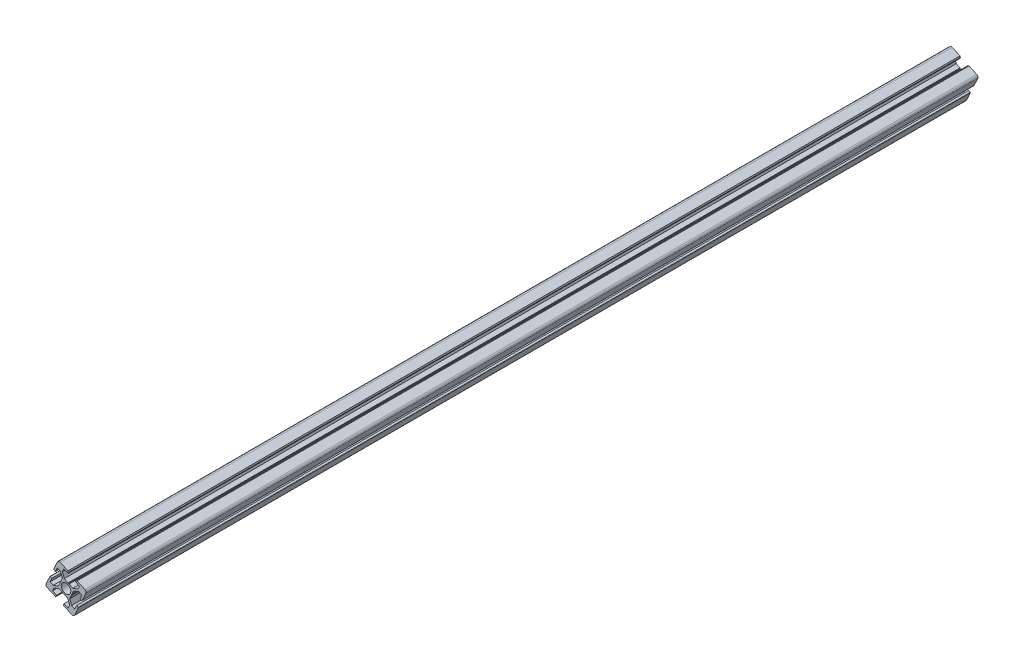
SolidWorks part; units mm, degrees
material "1060 Alloy"
ref_plane "Front" through (0, 0, 0) normal (0, 0, 1) x (1, 0, 0)
ref_plane "Top" through (0, 0, 0) normal (0, 1, 0) x (1, 0, 0)
ref_plane "Right" through (0, 0, 0) normal (1, 0, 0) x (0, 0, -1)
sketch "Sketch1" plane through (0, 0, 0) normal (0, 0, 1) x (1, 0, 0)
  line L0 (-8.2163, 18.0691) -> (-11.8426, 10.1609)
  line L1 (-11.6949, 9.7631) -> (-10.1496, 9.0546)
  line L2 (-10.1496, 9.0546) -> (-8.3782, 12.9178)
  line L3 (-8.3782, 12.9178) -> (-5.346, 11.5274)
  line L4 (-5.346, 11.5274) -> (-3.5425, 6.6693)
  line L5 (-3.5425, 6.6693) -> (-5.2374, 2.9732)
  line L6 (-5.2374, 2.9732) -> (-5.1813, 2.3758)
  line L7 (-5.1813, 2.3758) -> (-5.6705, 2.0286)
  line L8 (-5.6705, 2.0286) -> (-7.3654, -1.6675)
  line L9 (-7.3654, -1.6675) -> (-12.2234, -3.471)
  line L10 (-12.2234, -3.471) -> (-15.2556, -2.0806)
  line L11 (-15.2556, -2.0806) -> (-13.4841, 1.7826)
  line L12 (-13.4841, 1.7826) -> (-15.0294, 2.4912)
  line L13 (-15.4272, 2.3436) -> (-19.0535, -5.5647)
  line L14 (-18.0691, -8.2163) -> (-10.1609, -11.8426)
  line L15 (-9.7631, -11.6949) -> (-9.0546, -10.1496)
  line L16 (-9.0546, -10.1496) -> (-12.9178, -8.3782)
  line L17 (-12.9178, -8.3782) -> (-11.5274, -5.346)
  line L18 (-11.5274, -5.346) -> (-6.6693, -3.5425)
  line L19 (-6.6693, -3.5425) -> (-2.9732, -5.2374)
  line L20 (-2.9732, -5.2374) -> (-2.3758, -5.1813)
  line L21 (1.9074, 15.6272) -> (-5.5647, 19.0535)
  line L22 (2.3758, 5.1813) -> (2.9732, 5.2374)
  line L23 (2.9732, 5.2374) -> (6.6693, 3.5425)
  line L24 (12.9178, 8.3782) -> (8.9517, 10.1968)
  line L26 (10.597, 11.6426) -> (18.0691, 8.2163)
  line L27 (11.5274, 5.346) -> (12.9178, 8.3782)
  line L28 (6.6693, 3.5425) -> (11.5274, 5.346)
  line L29 (-2.0286, -5.6705) -> (-2.3758, -5.1813)
  line L30 (1.6675, -7.3654) -> (-2.0286, -5.6705)
  line L31 (3.471, -12.2234) -> (1.6675, -7.3654)
  line L32 (2.0806, -15.2556) -> (3.471, -12.2234)
  line L33 (-1.7826, -13.4841) -> (2.0806, -15.2556)
  line L34 (2.3758, 5.1813) -> (2.0286, 5.6705)
  line L35 (2.0286, 5.6705) -> (-1.6675, 7.3654)
  line L36 (-1.6675, 7.3654) -> (-3.471, 12.2234)
  line L37 (-3.471, 12.2234) -> (-2.0806, 15.2556)
  line L38 (-2.0806, 15.2556) -> (1.8855, 13.437)
  line L40 (2.3758, 5.1813) -> (-2.3758, -5.1813) construction
  line L41 (-2.4912, -15.0294) -> (-1.7826, -13.4841)
  line L42 (5.5647, -19.0535) -> (-2.3436, -15.4272)
  line L43 (11.8426, -10.1609) -> (8.2163, -18.0691)
  line L44 (10.1496, -9.0546) -> (11.6949, -9.7631)
  line L45 (8.3782, -12.9178) -> (10.1496, -9.0546)
  line L46 (5.346, -11.5274) -> (8.3782, -12.9178)
  line L47 (3.5425, -6.6693) -> (5.346, -11.5274)
  line L48 (5.2374, -2.9732) -> (3.5425, -6.6693)
  line L49 (5.1813, -2.3758) -> (5.2374, -2.9732)
  line L50 (5.6705, -2.0286) -> (5.1813, -2.3758)
  line L51 (7.3654, 1.6675) -> (5.6705, -2.0286)
  line L52 (12.2234, 3.471) -> (7.3654, 1.6675)
  line L53 (15.2556, 2.0806) -> (12.2234, 3.471)
  line L54 (13.4841, -1.7826) -> (15.2556, 2.0806)
  line L55 (15.0294, -2.4912) -> (13.4841, -1.7826)
  line L56 (19.0535, 5.5647) -> (15.4272, -2.3436)
  line L57 (1.8855, 13.437) -> (2.3469, 14.4432)
  line L58 (2.3469, 14.4432) -> (1.9074, 15.6272)
  line L59 (8.9517, 10.1968) -> (9.4131, 11.2031)
  line L60 (9.4131, 11.2031) -> (10.597, 11.6426)
  arc A0 (-5.5647, 19.0535) -> (-8.2163, 18.0691) centre (-6.3983, 17.2355) ccw
  arc A1 (-11.8426, 10.1609) -> (-11.6949, 9.7631) centre (-11.5699, 10.0358) ccw
  arc A2 (-15.0294, 2.4912) -> (-15.4272, 2.3436) centre (-15.1545, 2.2185) ccw
  arc A3 (-19.0535, -5.5647) -> (-18.0691, -8.2163) centre (-17.2355, -6.3983) ccw
  arc A4 (-10.1609, -11.8426) -> (-9.7631, -11.6949) centre (-10.0358, -11.5699) ccw
  arc A6 (-2.3436, -15.4272) -> (-2.4912, -15.0294) centre (-2.2185, -15.1545) cw
  arc A7 (8.2163, -18.0691) -> (5.5647, -19.0535) centre (6.3983, -17.2355) cw
  arc A8 (11.6949, -9.7631) -> (11.8426, -10.1609) centre (11.5699, -10.0358) cw
  arc A10 (15.4272, -2.3436) -> (15.0294, -2.4912) centre (15.1545, -2.2185) cw
  arc A11 (18.0691, 8.2163) -> (19.0535, 5.5647) centre (17.2355, 6.3983) cw
  dimension "D1" = 45
  dimension "D2" = 30
extrude "Boss-Extrude1" add sketch "Sketch1" along normal blind 2000
scale "Scale1" scale about centroid uniform scaling yes scale factor 3
sketch "Sketch2" plane through (0, 0, -2000) normal (0, 0, -1) x (-1, 0, 0)
  circle A0 centre (0, 0) radius 115.0478
extrude "Cut-Extrude1" cut sketch "Sketch2" against normal blind 1600
sketch "Sketch3" plane through (0, 0, 4000) normal (0, 0, 1) x (1, 0, 0)
  circle A0 centre (0, 0) radius 13.75
  dimension "D1" = 27.5
extrude "Cut-Extrude2" cut sketch "Sketch3" against normal through all
scale "Scale2" bodies to scale 104 scale about centroid uniform scaling yes scale factor 0.466667
sketch "Sketch6" plane through (0, 0, 773.3333) normal (0, 0, -1) x (-1, 0, 0)
  line L58 (7.7891, 26.678) -> (-2.6718, 21.8811)
  line L59 (-2.6718, 21.8811) -> (-3.2872, 20.2236)
  line L60 (-3.2872, 20.2236) -> (-2.6412, 18.8149)
  line L61 (-2.6412, 18.8149) -> (2.9114, 21.361)
  line L62 (2.9114, 21.361) -> (4.858, 17.1159)
  line L63 (4.858, 17.1159) -> (2.3331, 10.3146)
  line L64 (2.3331, 10.3146) -> (-2.8414, 7.9419)
  line L65 (-2.8414, 7.9419) -> (-3.3276, 7.2569)
  line L66 (-3.3276, 7.2569) -> (-4.1639, 7.3354)
  line L67 (-4.1639, 7.3354) -> (-9.3385, 4.9626)
  line L68 (-9.3385, 4.9626) -> (-16.1397, 7.4875)
  line L69 (-16.1397, 7.4875) -> (-18.0863, 11.7325)
  line L70 (-18.0863, 11.7325) -> (-12.5338, 14.2786)
  line L71 (-12.5338, 14.2786) -> (-13.1797, 15.6874)
  line L72 (-13.1797, 15.6874) -> (-14.8373, 16.3027)
  line L73 (-14.8373, 16.3027) -> (-25.2982, 11.5059)
  line L74 (-26.6763, 7.7936) -> (-21.5995, -3.2779)
  line L75 (-21.0426, -3.4846) -> (-18.8792, -2.4926)
  line L76 (-18.8792, -2.4926) -> (-21.3593, 2.9159)
  line L77 (-21.3593, 2.9159) -> (-17.1142, 4.8625)
  line L78 (-17.1142, 4.8625) -> (-10.3129, 2.3377)
  line L79 (-10.3129, 2.3377) -> (-7.9402, -2.8369)
  line L80 (-7.9402, -2.8369) -> (-7.2552, -3.3231)
  line L81 (-7.2552, -3.3231) -> (-7.3337, -4.1594)
  line L82 (-7.3337, -4.1594) -> (-4.961, -9.334)
  line L83 (-4.961, -9.334) -> (-7.4858, -16.1352)
  line L84 (-7.4858, -16.1352) -> (-11.7309, -18.0818)
  line L85 (-11.7309, -18.0818) -> (-14.2109, -12.6733)
  line L86 (-14.2109, -12.6733) -> (-16.3743, -13.6653)
  line L87 (-16.581, -14.2221) -> (-11.5042, -25.2936)
  line L88 (-7.7919, -26.6717) -> (3.2796, -21.5949)
  line L89 (3.4863, -21.0381) -> (2.4943, -18.8747)
  line L90 (2.4943, -18.8747) -> (-2.9142, -21.3547)
  line L91 (-2.9142, -21.3547) -> (-4.8608, -17.1097)
  line L92 (-4.8608, -17.1097) -> (-2.336, -10.3084)
  line L93 (-2.336, -10.3084) -> (2.8386, -7.9356)
  line L94 (2.8386, -7.9356) -> (3.3248, -7.2506)
  line L95 (3.3248, -7.2506) -> (4.1611, -7.3292)
  line L96 (4.1611, -7.3292) -> (9.3356, -4.9564)
  line L97 (9.3356, -4.9564) -> (16.1369, -7.4812)
  line L98 (16.1369, -7.4812) -> (18.0835, -11.7263)
  line L99 (18.0835, -11.7263) -> (12.675, -14.2064)
  line L100 (12.675, -14.2064) -> (13.667, -16.3698)
  line L101 (14.2238, -16.5765) -> (25.2953, -11.4997)
  line L102 (26.6734, -7.7874) -> (21.5966, 3.2841)
  line L103 (21.0398, 3.4908) -> (18.8764, 2.4988)
  line L104 (18.8764, 2.4988) -> (21.3564, -2.9097)
  line L105 (21.3564, -2.9097) -> (17.1113, -4.8563)
  line L106 (17.1113, -4.8563) -> (10.3101, -2.3315)
  line L107 (10.3101, -2.3315) -> (7.9373, 2.8431)
  line L108 (7.9373, 2.8431) -> (7.2523, 3.3293)
  line L109 (7.2523, 3.3293) -> (7.3309, 4.1656)
  line L110 (7.3309, 4.1656) -> (4.9581, 9.3402)
  line L111 (4.9581, 9.3402) -> (7.4829, 16.1414)
  line L112 (7.4829, 16.1414) -> (11.728, 18.088)
  line L113 (11.728, 18.088) -> (14.208, 12.6795)
  line L114 (14.208, 12.6795) -> (16.3714, 13.6715)
  line L115 (16.5782, 14.2284) -> (11.5014, 25.2999)
  line L116 (7.7891, 26.678) -> (-2.6718, 21.8811)
  line L117 (-2.6718, 21.8811) -> (-3.2872, 20.2236)
  line L118 (-3.2872, 20.2236) -> (-2.6412, 18.8149)
  line L119 (-2.6412, 18.8149) -> (2.9114, 21.361)
  line L120 (2.9114, 21.361) -> (4.858, 17.1159)
  line L121 (4.858, 17.1159) -> (2.3331, 10.3146)
  line L122 (2.3331, 10.3146) -> (-2.8414, 7.9419)
  line L123 (-2.8414, 7.9419) -> (-3.3276, 7.2569)
  line L124 (-3.3276, 7.2569) -> (-4.1639, 7.3354)
  line L125 (-4.1639, 7.3354) -> (-9.3385, 4.9626)
  line L126 (-9.3385, 4.9626) -> (-16.1397, 7.4875)
  line L127 (-16.1397, 7.4875) -> (-18.0863, 11.7325)
  line L128 (-18.0863, 11.7325) -> (-12.5338, 14.2786)
  line L129 (-12.5338, 14.2786) -> (-13.1797, 15.6874)
  line L130 (-13.1797, 15.6874) -> (-14.8373, 16.3027)
  line L131 (-14.8373, 16.3027) -> (-25.2982, 11.5059)
  line L132 (-26.6763, 7.7936) -> (-21.5995, -3.2779)
  line L133 (-21.0426, -3.4846) -> (-18.8792, -2.4926)
  line L134 (-18.8792, -2.4926) -> (-21.3593, 2.9159)
  line L135 (-21.3593, 2.9159) -> (-17.1142, 4.8625)
  line L136 (-17.1142, 4.8625) -> (-10.3129, 2.3377)
  line L137 (-10.3129, 2.3377) -> (-7.9402, -2.8369)
  line L138 (-7.9402, -2.8369) -> (-7.2552, -3.3231)
  line L139 (-7.2552, -3.3231) -> (-7.3337, -4.1594)
  line L140 (-7.3337, -4.1594) -> (-4.961, -9.334)
  line L141 (-4.961, -9.334) -> (-7.4858, -16.1352)
  line L142 (-7.4858, -16.1352) -> (-11.7309, -18.0818)
  line L143 (-11.7309, -18.0818) -> (-14.2109, -12.6733)
  line L144 (-14.2109, -12.6733) -> (-16.3743, -13.6653)
  line L145 (-16.581, -14.2221) -> (-11.5042, -25.2936)
  line L146 (-7.7919, -26.6717) -> (3.2796, -21.5949)
  line L147 (3.4863, -21.0381) -> (2.4943, -18.8747)
  line L148 (2.4943, -18.8747) -> (-2.9142, -21.3547)
  line L149 (-2.9142, -21.3547) -> (-4.8608, -17.1097)
  line L150 (-4.8608, -17.1097) -> (-2.336, -10.3084)
  line L151 (-2.336, -10.3084) -> (2.8386, -7.9356)
  line L152 (2.8386, -7.9356) -> (3.3248, -7.2506)
  line L153 (3.3248, -7.2506) -> (4.1611, -7.3292)
  line L154 (4.1611, -7.3292) -> (9.3356, -4.9564)
  line L155 (9.3356, -4.9564) -> (16.1369, -7.4812)
  line L156 (16.1369, -7.4812) -> (18.0835, -11.7263)
  line L157 (18.0835, -11.7263) -> (12.675, -14.2064)
  line L158 (12.675, -14.2064) -> (13.667, -16.3698)
  line L159 (14.2238, -16.5765) -> (25.2953, -11.4997)
  line L160 (26.6734, -7.7874) -> (21.5966, 3.2841)
  line L161 (21.0398, 3.4908) -> (18.8764, 2.4988)
  line L162 (18.8764, 2.4988) -> (21.3564, -2.9097)
  line L163 (21.3564, -2.9097) -> (17.1113, -4.8563)
  line L164 (17.1113, -4.8563) -> (10.3101, -2.3315)
  line L165 (10.3101, -2.3315) -> (7.9373, 2.8431)
  line L166 (7.9373, 2.8431) -> (7.2523, 3.3293)
  line L167 (7.2523, 3.3293) -> (7.3309, 4.1656)
  line L168 (7.3309, 4.1656) -> (4.9581, 9.3402)
  line L169 (4.9581, 9.3402) -> (7.4829, 16.1414)
  line L170 (7.4829, 16.1414) -> (11.728, 18.088)
  line L171 (11.728, 18.088) -> (14.208, 12.6795)
  line L172 (14.208, 12.6795) -> (16.3714, 13.6715)
  line L173 (16.5782, 14.2284) -> (11.5014, 25.2999)
  arc A10 (11.5014, 25.2999) -> (7.7891, 26.678) centre (8.9562, 24.1328) ccw
  arc A11 (-25.2982, 11.5059) -> (-26.6763, 7.7936) centre (-24.1311, 8.9607) ccw
  arc A12 (-21.5995, -3.2779) -> (-21.0426, -3.4846) centre (-21.2177, -3.1028) ccw
  arc A13 (-16.3743, -13.6653) -> (-16.581, -14.2221) centre (-16.1992, -14.0471) ccw
  arc A14 (-11.5042, -25.2936) -> (-7.7919, -26.6717) centre (-8.959, -24.1266) ccw
  arc A15 (3.2796, -21.5949) -> (3.4863, -21.0381) centre (3.1045, -21.2132) ccw
  arc A16 (13.667, -16.3698) -> (14.2238, -16.5765) centre (14.0488, -16.1947) ccw
  arc A17 (25.2953, -11.4997) -> (26.6734, -7.7874) centre (24.1282, -8.9545) ccw
  arc A18 (21.5966, 3.2841) -> (21.0398, 3.4908) centre (21.2148, 3.109) ccw
  arc A19 (16.3714, 13.6715) -> (16.5782, 14.2284) centre (16.1964, 14.0533) ccw
  arc A20 (11.5014, 25.2999) -> (7.7891, 26.678) centre (8.9562, 24.1328) ccw
  arc A21 (-25.2982, 11.5059) -> (-26.6763, 7.7936) centre (-24.1311, 8.9607) ccw
  arc A22 (-21.5995, -3.2779) -> (-21.0426, -3.4846) centre (-21.2177, -3.1028) ccw
  arc A23 (-16.3743, -13.6653) -> (-16.581, -14.2221) centre (-16.1992, -14.0471) ccw
  arc A24 (-11.5042, -25.2936) -> (-7.7919, -26.6717) centre (-8.959, -24.1266) ccw
  arc A25 (3.2796, -21.5949) -> (3.4863, -21.0381) centre (3.1045, -21.2132) ccw
  arc A26 (13.667, -16.3698) -> (14.2238, -16.5765) centre (14.0488, -16.1947) ccw
  arc A27 (25.2953, -11.4997) -> (26.6734, -7.7874) centre (24.1282, -8.9545) ccw
  arc A28 (21.5966, 3.2841) -> (21.0398, 3.4908) centre (21.2148, 3.109) ccw
  arc A29 (16.3714, 13.6715) -> (16.5782, 14.2284) centre (16.1964, 14.0533) ccw
  dimension "D1" = 0
extrude "Cut-Extrude3" cut sketch "Sketch6" against normal blind 53.3
sketch "Sketch7" plane through (0, 0, 826.6333) normal (0, 0, -1) x (-1, 0, 0)
  line L58 (7.7891, 26.678) -> (-2.6718, 21.8811)
  line L59 (-2.6718, 21.8811) -> (-3.2872, 20.2236)
  line L60 (-3.2872, 20.2236) -> (-2.6412, 18.8149)
  line L61 (-2.6412, 18.8149) -> (2.9114, 21.361)
  line L62 (2.9114, 21.361) -> (4.858, 17.1159)
  line L63 (4.858, 17.1159) -> (2.3331, 10.3146)
  line L64 (2.3331, 10.3146) -> (-2.8414, 7.9419)
  line L65 (-2.8414, 7.9419) -> (-3.3276, 7.2569)
  line L66 (-3.3276, 7.2569) -> (-4.1639, 7.3354)
  line L67 (-4.1639, 7.3354) -> (-9.3385, 4.9626)
  line L68 (-9.3385, 4.9626) -> (-16.1397, 7.4875)
  line L69 (-16.1397, 7.4875) -> (-18.0863, 11.7325)
  line L70 (-18.0863, 11.7325) -> (-12.5338, 14.2786)
  line L71 (-12.5338, 14.2786) -> (-13.1797, 15.6874)
  line L72 (-13.1797, 15.6874) -> (-14.8373, 16.3027)
  line L73 (-14.8373, 16.3027) -> (-25.2982, 11.5059)
  line L74 (-26.6763, 7.7936) -> (-21.5995, -3.2779)
  line L75 (-21.0426, -3.4846) -> (-18.8792, -2.4926)
  line L76 (-18.8792, -2.4926) -> (-21.3593, 2.9159)
  line L77 (-21.3593, 2.9159) -> (-17.1142, 4.8625)
  line L78 (-17.1142, 4.8625) -> (-10.3129, 2.3377)
  line L79 (-10.3129, 2.3377) -> (-7.9402, -2.8369)
  line L80 (-7.9402, -2.8369) -> (-7.2552, -3.3231)
  line L81 (-7.2552, -3.3231) -> (-7.3337, -4.1594)
  line L82 (-7.3337, -4.1594) -> (-4.961, -9.334)
  line L83 (-4.961, -9.334) -> (-7.4858, -16.1352)
  line L84 (-7.4858, -16.1352) -> (-11.7309, -18.0818)
  line L85 (-11.7309, -18.0818) -> (-14.2109, -12.6733)
  line L86 (-14.2109, -12.6733) -> (-16.3743, -13.6653)
  line L87 (-16.581, -14.2221) -> (-11.5042, -25.2936)
  line L88 (-7.7919, -26.6717) -> (3.2796, -21.5949)
  line L89 (3.4863, -21.0381) -> (2.4943, -18.8747)
  line L90 (2.4943, -18.8747) -> (-2.9142, -21.3547)
  line L91 (-2.9142, -21.3547) -> (-4.8608, -17.1097)
  line L92 (-4.8608, -17.1097) -> (-2.336, -10.3084)
  line L93 (-2.336, -10.3084) -> (2.8386, -7.9356)
  line L94 (2.8386, -7.9356) -> (3.3248, -7.2506)
  line L95 (3.3248, -7.2506) -> (4.1611, -7.3292)
  line L96 (4.1611, -7.3292) -> (9.3356, -4.9564)
  line L97 (9.3356, -4.9564) -> (16.1369, -7.4812)
  line L98 (16.1369, -7.4812) -> (18.0835, -11.7263)
  line L99 (18.0835, -11.7263) -> (12.675, -14.2064)
  line L100 (12.675, -14.2064) -> (13.667, -16.3698)
  line L101 (14.2238, -16.5765) -> (25.2953, -11.4997)
  line L102 (26.6734, -7.7874) -> (21.5966, 3.2841)
  line L103 (21.0398, 3.4908) -> (18.8764, 2.4988)
  line L104 (18.8764, 2.4988) -> (21.3564, -2.9097)
  line L105 (21.3564, -2.9097) -> (17.1113, -4.8563)
  line L106 (17.1113, -4.8563) -> (10.3101, -2.3315)
  line L107 (10.3101, -2.3315) -> (7.9373, 2.8431)
  line L108 (7.9373, 2.8431) -> (7.2523, 3.3293)
  line L109 (7.2523, 3.3293) -> (7.3309, 4.1656)
  line L110 (7.3309, 4.1656) -> (4.9581, 9.3402)
  line L111 (4.9581, 9.3402) -> (7.4829, 16.1414)
  line L112 (7.4829, 16.1414) -> (11.728, 18.088)
  line L113 (11.728, 18.088) -> (14.208, 12.6795)
  line L114 (14.208, 12.6795) -> (16.3714, 13.6715)
  line L115 (16.5782, 14.2284) -> (11.5014, 25.2999)
  line L116 (7.7891, 26.678) -> (-2.6718, 21.8811)
  line L117 (-2.6718, 21.8811) -> (-3.2872, 20.2236)
  line L118 (-3.2872, 20.2236) -> (-2.6412, 18.8149)
  line L119 (-2.6412, 18.8149) -> (2.9114, 21.361)
  line L120 (2.9114, 21.361) -> (4.858, 17.1159)
  line L121 (4.858, 17.1159) -> (2.3331, 10.3146)
  line L122 (2.3331, 10.3146) -> (-2.8414, 7.9419)
  line L123 (-2.8414, 7.9419) -> (-3.3276, 7.2569)
  line L124 (-3.3276, 7.2569) -> (-4.1639, 7.3354)
  line L125 (-4.1639, 7.3354) -> (-9.3385, 4.9626)
  line L126 (-9.3385, 4.9626) -> (-16.1397, 7.4875)
  line L127 (-16.1397, 7.4875) -> (-18.0863, 11.7325)
  line L128 (-18.0863, 11.7325) -> (-12.5338, 14.2786)
  line L129 (-12.5338, 14.2786) -> (-13.1797, 15.6874)
  line L130 (-13.1797, 15.6874) -> (-14.8373, 16.3027)
  line L131 (-14.8373, 16.3027) -> (-25.2982, 11.5059)
  line L132 (-26.6763, 7.7936) -> (-21.5995, -3.2779)
  line L133 (-21.0426, -3.4846) -> (-18.8792, -2.4926)
  line L134 (-18.8792, -2.4926) -> (-21.3593, 2.9159)
  line L135 (-21.3593, 2.9159) -> (-17.1142, 4.8625)
  line L136 (-17.1142, 4.8625) -> (-10.3129, 2.3377)
  line L137 (-10.3129, 2.3377) -> (-7.9402, -2.8369)
  line L138 (-7.9402, -2.8369) -> (-7.2552, -3.3231)
  line L139 (-7.2552, -3.3231) -> (-7.3337, -4.1594)
  line L140 (-7.3337, -4.1594) -> (-4.961, -9.334)
  line L141 (-4.961, -9.334) -> (-7.4858, -16.1352)
  line L142 (-7.4858, -16.1352) -> (-11.7309, -18.0818)
  line L143 (-11.7309, -18.0818) -> (-14.2109, -12.6733)
  line L144 (-14.2109, -12.6733) -> (-16.3743, -13.6653)
  line L145 (-16.581, -14.2221) -> (-11.5042, -25.2936)
  line L146 (-7.7919, -26.6717) -> (3.2796, -21.5949)
  line L147 (3.4863, -21.0381) -> (2.4943, -18.8747)
  line L148 (2.4943, -18.8747) -> (-2.9142, -21.3547)
  line L149 (-2.9142, -21.3547) -> (-4.8608, -17.1097)
  line L150 (-4.8608, -17.1097) -> (-2.336, -10.3084)
  line L151 (-2.336, -10.3084) -> (2.8386, -7.9356)
  line L152 (2.8386, -7.9356) -> (3.3248, -7.2506)
  line L153 (3.3248, -7.2506) -> (4.1611, -7.3292)
  line L154 (4.1611, -7.3292) -> (9.3356, -4.9564)
  line L155 (9.3356, -4.9564) -> (16.1369, -7.4812)
  line L156 (16.1369, -7.4812) -> (18.0835, -11.7263)
  line L157 (18.0835, -11.7263) -> (12.675, -14.2064)
  line L158 (12.675, -14.2064) -> (13.667, -16.3698)
  line L159 (14.2238, -16.5765) -> (25.2953, -11.4997)
  line L160 (26.6734, -7.7874) -> (21.5966, 3.2841)
  line L161 (21.0398, 3.4908) -> (18.8764, 2.4988)
  line L162 (18.8764, 2.4988) -> (21.3564, -2.9097)
  line L163 (21.3564, -2.9097) -> (17.1113, -4.8563)
  line L164 (17.1113, -4.8563) -> (10.3101, -2.3315)
  line L165 (10.3101, -2.3315) -> (7.9373, 2.8431)
  line L166 (7.9373, 2.8431) -> (7.2523, 3.3293)
  line L167 (7.2523, 3.3293) -> (7.3309, 4.1656)
  line L168 (7.3309, 4.1656) -> (4.9581, 9.3402)
  line L169 (4.9581, 9.3402) -> (7.4829, 16.1414)
  line L170 (7.4829, 16.1414) -> (11.728, 18.088)
  line L171 (11.728, 18.088) -> (14.208, 12.6795)
  line L172 (14.208, 12.6795) -> (16.3714, 13.6715)
  line L173 (16.5782, 14.2284) -> (11.5014, 25.2999)
  arc A10 (11.5014, 25.2999) -> (7.7891, 26.678) centre (8.9562, 24.1328) ccw
  arc A11 (-25.2982, 11.5059) -> (-26.6763, 7.7936) centre (-24.1311, 8.9607) ccw
  arc A12 (-21.5995, -3.2779) -> (-21.0426, -3.4846) centre (-21.2177, -3.1028) ccw
  arc A13 (-16.3743, -13.6653) -> (-16.581, -14.2221) centre (-16.1992, -14.0471) ccw
  arc A14 (-11.5042, -25.2936) -> (-7.7919, -26.6717) centre (-8.959, -24.1266) ccw
  arc A15 (3.2796, -21.5949) -> (3.4863, -21.0381) centre (3.1045, -21.2132) ccw
  arc A16 (13.667, -16.3698) -> (14.2238, -16.5765) centre (14.0488, -16.1947) ccw
  arc A17 (25.2953, -11.4997) -> (26.6734, -7.7874) centre (24.1282, -8.9545) ccw
  arc A18 (21.5966, 3.2841) -> (21.0398, 3.4908) centre (21.2148, 3.109) ccw
  arc A19 (16.3714, 13.6715) -> (16.5782, 14.2284) centre (16.1964, 14.0533) ccw
  arc A20 (11.5014, 25.2999) -> (7.7891, 26.678) centre (8.9562, 24.1328) ccw
  arc A21 (-25.2982, 11.5059) -> (-26.6763, 7.7936) centre (-24.1311, 8.9607) ccw
  arc A22 (-21.5995, -3.2779) -> (-21.0426, -3.4846) centre (-21.2177, -3.1028) ccw
  arc A23 (-16.3743, -13.6653) -> (-16.581, -14.2221) centre (-16.1992, -14.0471) ccw
  arc A24 (-11.5042, -25.2936) -> (-7.7919, -26.6717) centre (-8.959, -24.1266) ccw
  arc A25 (3.2796, -21.5949) -> (3.4863, -21.0381) centre (3.1045, -21.2132) ccw
  arc A26 (13.667, -16.3698) -> (14.2238, -16.5765) centre (14.0488, -16.1947) ccw
  arc A27 (25.2953, -11.4997) -> (26.6734, -7.7874) centre (24.1282, -8.9545) ccw
  arc A28 (21.5966, 3.2841) -> (21.0398, 3.4908) centre (21.2148, 3.109) ccw
  arc A29 (16.3714, 13.6715) -> (16.5782, 14.2284) centre (16.1964, 14.0533) ccw
  dimension "D1" = 0
extrude "Cut-Extrude4" cut sketch "Sketch7" against normal blind 800
